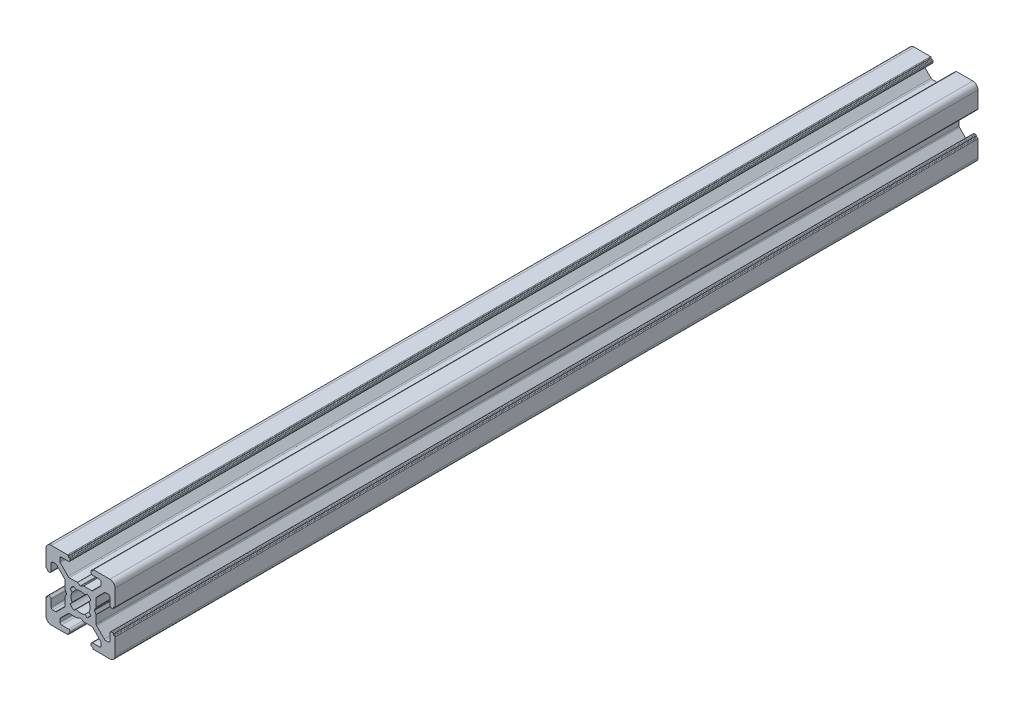
SolidWorks part; units mm, degrees
ref_plane "Płaszczyzna przednia" through (0, 0, 0) normal (0, 0, 1) x (1, 0, 0)
ref_plane "Płaszczyzna górna" through (0, 0, 0) normal (0, 1, 0) x (1, 0, 0)
ref_plane "Płaszczyzna prawa" through (0, 0, 0) normal (1, 0, 0) x (0, 0, -1)
sketch "Croquis" plane through (0, 0, 0) normal (0, 0, 1) x (1, 0, 0)
  line L0 (7.0078, -1.8401) -> (7.5547, -2.4918)
  line L1 (7.5547, -5.0082) -> (7.0078, -5.6599)
  line L2 (8.0861, -6.7396) -> (8.7418, -6.1953)
  line L3 (11.2582, -6.1953) -> (11.9139, -6.7396)
  line L4 (12.9922, -5.6599) -> (12.4453, -5.0082)
  line L5 (12.4453, -2.4918) -> (12.9922, -1.8401)
  line L6 (11.9139, -0.7604) -> (11.2582, -1.3047)
  line L7 (8.7418, -1.3047) -> (8.0861, -0.7604)
  line L8 (6.25, 6.25) -> (1.5, 6.25)
  line L9 (6.45, 5.95) -> (6.45, 6.05)
  line L10 (6.8, 5.75) -> (6.65, 5.75)
  line L11 (7, 5.25) -> (7, 5.55)
  line L12 (4.5, 4.75) -> (6.5, 4.75)
  line L13 (4, 3.5178) -> (4, 4.25)
  line L14 (6.4142, 0.8964) -> (4.1464, 3.1642)
  line L15 (9.0464, 0.75) -> (6.7678, 0.75)
  line L16 (9.9, 0.2881) -> (9.1464, 0.7232)
  line L17 (10.8536, 0.7232) -> (10.1, 0.2881)
  line L18 (13.2322, 0.75) -> (10.9536, 0.75)
  line L19 (15.8536, 3.1642) -> (13.5858, 0.8964)
  line L20 (16, 4.25) -> (16, 3.5178)
  line L21 (13.5, 4.75) -> (15.5, 4.75)
  line L22 (13, 5.55) -> (13, 5.25)
  line L23 (13.35, 5.75) -> (13.2, 5.75)
  line L24 (13.55, 6.05) -> (13.55, 5.95)
  line L25 (18.5, 6.25) -> (13.75, 6.25)
  line L26 (20, 0) -> (20, 4.75)
  line L27 (19.7, -0.2) -> (19.8, -0.2)
  line L28 (19.5, -0.55) -> (19.5, -0.4)
  line L29 (19, -0.75) -> (19.3, -0.75)
  line L30 (18.5, 1.75) -> (18.5, -0.25)
  line L31 (17.2678, 2.25) -> (18, 2.25)
  line L32 (14.6464, -0.1642) -> (16.9142, 2.1036)
  line L33 (14.5, -2.7964) -> (14.5, -0.5178)
  line L34 (14.0381, -3.65) -> (14.4732, -2.8964)
  line L35 (14.4732, -4.6036) -> (14.0381, -3.85)
  line L36 (14.5, -6.9822) -> (14.5, -4.7036)
  line L37 (16.9142, -9.6036) -> (14.6464, -7.3358)
  line L38 (18, -9.75) -> (17.2678, -9.75)
  line L39 (18.5, -7.25) -> (18.5, -9.25)
  line L40 (19.3, -6.75) -> (19, -6.75)
  line L41 (19.5, -7.1) -> (19.5, -6.95)
  line L42 (19.8, -7.3) -> (19.7, -7.3)
  line L43 (20, -12.25) -> (20, -7.5)
  line L44 (13.75, -13.75) -> (18.5, -13.75)
  line L45 (13.55, -13.45) -> (13.55, -13.55)
  line L46 (13.2, -13.25) -> (13.35, -13.25)
  line L47 (13, -12.75) -> (13, -13.05)
  line L48 (15.5, -12.25) -> (13.5, -12.25)
  line L49 (16, -11.0178) -> (16, -11.75)
  line L50 (13.5858, -8.3964) -> (15.8536, -10.6642)
  line L51 (10.9536, -8.25) -> (13.2322, -8.25)
  line L52 (10.1, -7.7881) -> (10.8536, -8.2232)
  line L53 (9.1464, -8.2232) -> (9.9, -7.7881)
  line L54 (6.7678, -8.25) -> (9.0464, -8.25)
  line L55 (4.1464, -10.6642) -> (6.4142, -8.3964)
  line L56 (4, -11.75) -> (4, -11.0178)
  line L57 (6.5, -12.25) -> (4.5, -12.25)
  line L58 (7, -13.05) -> (7, -12.75)
  line L59 (6.65, -13.25) -> (6.8, -13.25)
  line L60 (6.45, -13.55) -> (6.45, -13.45)
  line L61 (1.5, -13.75) -> (6.25, -13.75)
  line L62 (0, -7.5) -> (0, -12.25)
  line L63 (0.3, -7.3) -> (0.2, -7.3)
  line L64 (0.5, -6.95) -> (0.5, -7.1)
  line L65 (1, -6.75) -> (0.7, -6.75)
  line L66 (1.5, -9.25) -> (1.5, -7.25)
  line L67 (2.7322, -9.75) -> (2, -9.75)
  line L68 (5.3536, -7.3358) -> (3.0858, -9.6036)
  line L69 (5.5, -4.7036) -> (5.5, -6.9822)
  line L70 (5.9619, -3.85) -> (5.5268, -4.6036)
  line L71 (5.5268, -2.8964) -> (5.9619, -3.65)
  line L72 (5.5, -0.5178) -> (5.5, -2.7964)
  line L73 (3.0858, 2.1036) -> (5.3536, -0.1642)
  line L74 (2, 2.25) -> (2.7322, 2.25)
  line L75 (1.5, -0.25) -> (1.5, 1.75)
  line L76 (0.7, -0.75) -> (1, -0.75)
  line L77 (0.5, -0.4) -> (0.5, -0.55)
  line L78 (0.2, -0.2) -> (0.3, -0.2)
  line L79 (0, 4.75) -> (0, 0)
  arc A0 (7.5547, -2.4918) -> (7.5547, -5.0082) centre (10, -3.75) ccw
  arc A1 (7.0078, -5.6599) -> (8.0861, -6.7396) centre (10, -3.75) ccw
  arc A2 (8.7418, -6.1953) -> (11.2582, -6.1953) centre (10, -3.75) ccw
  arc A3 (11.9139, -6.7396) -> (12.9922, -5.6599) centre (10, -3.75) ccw
  arc A4 (12.4453, -5.0082) -> (12.4453, -2.4918) centre (10, -3.75) ccw
  arc A5 (12.9922, -1.8401) -> (11.9139, -0.7604) centre (10, -3.75) ccw
  arc A6 (11.2582, -1.3047) -> (8.7418, -1.3047) centre (10, -3.75) ccw
  arc A7 (8.0861, -0.7604) -> (7.0078, -1.8401) centre (10, -3.75) ccw
  arc A8 (6.45, 6.05) -> (6.25, 6.25) centre (6.25, 6.05) ccw
  arc A9 (6.45, 5.95) -> (6.65, 5.75) centre (6.65, 5.95) ccw
  arc A10 (7, 5.55) -> (6.8, 5.75) centre (6.8, 5.55) ccw
  arc A11 (6.5, 4.75) -> (7, 5.25) centre (6.5, 5.25) ccw
  arc A12 (4.5, 4.75) -> (4, 4.25) centre (4.5, 4.25) ccw
  arc A13 (4, 3.5178) -> (4.1464, 3.1642) centre (4.5, 3.5178) ccw
  arc A14 (6.4142, 0.8964) -> (6.7678, 0.75) centre (6.7678, 1.25) ccw
  arc A15 (9.1464, 0.7232) -> (9.0464, 0.75) centre (9.0464, 0.55) ccw
  arc A16 (9.9, 0.2881) -> (10.1, 0.2881) centre (10, 0.4613) ccw
  arc A17 (10.9536, 0.75) -> (10.8536, 0.7232) centre (10.9536, 0.55) ccw
  arc A18 (13.2322, 0.75) -> (13.5858, 0.8964) centre (13.2322, 1.25) ccw
  arc A19 (15.8536, 3.1642) -> (16, 3.5178) centre (15.5, 3.5178) ccw
  arc A20 (16, 4.25) -> (15.5, 4.75) centre (15.5, 4.25) ccw
  arc A21 (13, 5.25) -> (13.5, 4.75) centre (13.5, 5.25) ccw
  arc A22 (13.2, 5.75) -> (13, 5.55) centre (13.2, 5.55) ccw
  arc A23 (13.35, 5.75) -> (13.55, 5.95) centre (13.35, 5.95) ccw
  arc A24 (13.75, 6.25) -> (13.55, 6.05) centre (13.75, 6.05) ccw
  arc A25 (20, 4.75) -> (18.5, 6.25) centre (18.5, 4.75) ccw
  arc A26 (19.8, -0.2) -> (20, 0) centre (19.8, 0) ccw
  arc A27 (19.7, -0.2) -> (19.5, -0.4) centre (19.7, -0.4) ccw
  arc A28 (19.3, -0.75) -> (19.5, -0.55) centre (19.3, -0.55) ccw
  arc A29 (18.5, -0.25) -> (19, -0.75) centre (19, -0.25) ccw
  arc A30 (18.5, 1.75) -> (18, 2.25) centre (18, 1.75) ccw
  arc A31 (17.2678, 2.25) -> (16.9142, 2.1036) centre (17.2678, 1.75) ccw
  arc A32 (14.6464, -0.1642) -> (14.5, -0.5178) centre (15, -0.5178) ccw
  arc A33 (14.4732, -2.8964) -> (14.5, -2.7964) centre (14.3, -2.7964) ccw
  arc A34 (14.0381, -3.65) -> (14.0381, -3.85) centre (14.2113, -3.75) ccw
  arc A35 (14.5, -4.7036) -> (14.4732, -4.6036) centre (14.3, -4.7036) ccw
  arc A36 (14.5, -6.9822) -> (14.6464, -7.3358) centre (15, -6.9822) ccw
  arc A37 (16.9142, -9.6036) -> (17.2678, -9.75) centre (17.2678, -9.25) ccw
  arc A38 (18, -9.75) -> (18.5, -9.25) centre (18, -9.25) ccw
  arc A39 (19, -6.75) -> (18.5, -7.25) centre (19, -7.25) ccw
  arc A40 (19.5, -6.95) -> (19.3, -6.75) centre (19.3, -6.95) ccw
  arc A41 (19.5, -7.1) -> (19.7, -7.3) centre (19.7, -7.1) ccw
  arc A42 (20, -7.5) -> (19.8, -7.3) centre (19.8, -7.5) ccw
  arc A43 (18.5, -13.75) -> (20, -12.25) centre (18.5, -12.25) ccw
  arc A44 (13.55, -13.55) -> (13.75, -13.75) centre (13.75, -13.55) ccw
  arc A45 (13.55, -13.45) -> (13.35, -13.25) centre (13.35, -13.45) ccw
  arc A46 (13, -13.05) -> (13.2, -13.25) centre (13.2, -13.05) ccw
  arc A47 (13.5, -12.25) -> (13, -12.75) centre (13.5, -12.75) ccw
  arc A48 (15.5, -12.25) -> (16, -11.75) centre (15.5, -11.75) ccw
  arc A49 (16, -11.0178) -> (15.8536, -10.6642) centre (15.5, -11.0178) ccw
  arc A50 (13.5858, -8.3964) -> (13.2322, -8.25) centre (13.2322, -8.75) ccw
  arc A51 (10.8536, -8.2232) -> (10.9536, -8.25) centre (10.9536, -8.05) ccw
  arc A52 (10.1, -7.7881) -> (9.9, -7.7881) centre (10, -7.9613) ccw
  arc A53 (9.0464, -8.25) -> (9.1464, -8.2232) centre (9.0464, -8.05) ccw
  arc A54 (6.7678, -8.25) -> (6.4142, -8.3964) centre (6.7678, -8.75) ccw
  arc A55 (4.1464, -10.6642) -> (4, -11.0178) centre (4.5, -11.0178) ccw
  arc A56 (4, -11.75) -> (4.5, -12.25) centre (4.5, -11.75) ccw
  arc A57 (7, -12.75) -> (6.5, -12.25) centre (6.5, -12.75) ccw
  arc A58 (6.8, -13.25) -> (7, -13.05) centre (6.8, -13.05) ccw
  arc A59 (6.65, -13.25) -> (6.45, -13.45) centre (6.65, -13.45) ccw
  arc A60 (6.25, -13.75) -> (6.45, -13.55) centre (6.25, -13.55) ccw
  arc A61 (0, -12.25) -> (1.5, -13.75) centre (1.5, -12.25) ccw
  arc A62 (0.2, -7.3) -> (0, -7.5) centre (0.2, -7.5) ccw
  arc A63 (0.3, -7.3) -> (0.5, -7.1) centre (0.3, -7.1) ccw
  arc A64 (0.7, -6.75) -> (0.5, -6.95) centre (0.7, -6.95) ccw
  arc A65 (1.5, -7.25) -> (1, -6.75) centre (1, -7.25) ccw
  arc A66 (1.5, -9.25) -> (2, -9.75) centre (2, -9.25) ccw
  arc A67 (2.7322, -9.75) -> (3.0858, -9.6036) centre (2.7322, -9.25) ccw
  arc A68 (5.3536, -7.3358) -> (5.5, -6.9822) centre (5, -6.9822) ccw
  arc A69 (5.5268, -4.6036) -> (5.5, -4.7036) centre (5.7, -4.7036) ccw
  arc A70 (5.9619, -3.85) -> (5.9619, -3.65) centre (5.7887, -3.75) ccw
  arc A71 (5.5, -2.7964) -> (5.5268, -2.8964) centre (5.7, -2.7964) ccw
  arc A72 (5.5, -0.5178) -> (5.3536, -0.1642) centre (5, -0.5178) ccw
  arc A73 (3.0858, 2.1036) -> (2.7322, 2.25) centre (2.7322, 1.75) ccw
  arc A74 (2, 2.25) -> (1.5, 1.75) centre (2, 1.75) ccw
  arc A75 (1, -0.75) -> (1.5, -0.25) centre (1, -0.25) ccw
  arc A76 (0.5, -0.55) -> (0.7, -0.75) centre (0.7, -0.55) ccw
  arc A77 (0.5, -0.4) -> (0.3, -0.2) centre (0.3, -0.4) ccw
  arc A78 (0, 0) -> (0.2, -0.2) centre (0.2, 0) ccw
  arc A79 (1.5, 6.25) -> (0, 4.75) centre (1.5, 4.75) ccw
  dimension "D4" = 2.75
  dimension "D1" = 20
  dimension "D2" = 20
  dimension "D3" = 6
extrude "Saliente_Extruir" add sketch "Croquis" along normal blind 250
